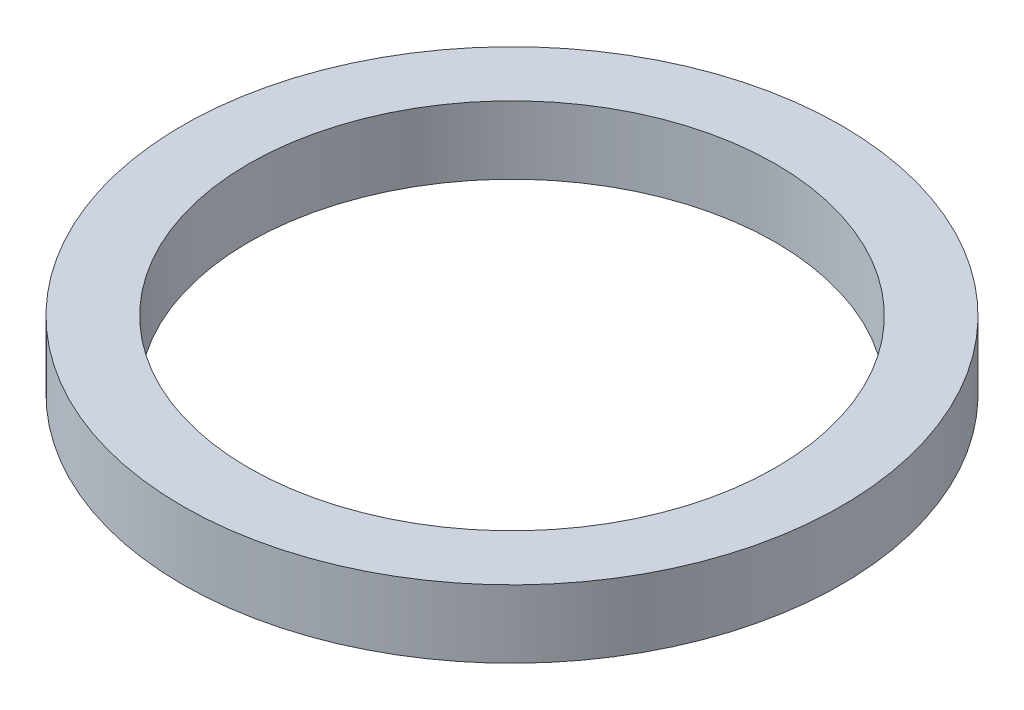
SolidWorks part; units mm, degrees
ref_plane "Front Plane" through (0, 0, 0) normal (0, 0, 1) x (1, 0, 0)
ref_plane "Top Plane" through (0, 0, 0) normal (0, 1, 0) x (1, 0, 0)
ref_plane "Right Plane" through (0, 0, 0) normal (1, 0, 0) x (0, 0, -1)
sketch "Sketch1" plane through (0, 0, 0) normal (0, 1, 0) x (1, 0, 0)
  circle A0 centre (0, 0) radius 12.7
  circle A1 centre (0, 0) radius 10.1473
  dimension "D1" = 25.4
  dimension "D2" = 20.2946
extrude "Boss-Extrude1" add sketch "Sketch1" along normal blind 2.6162
